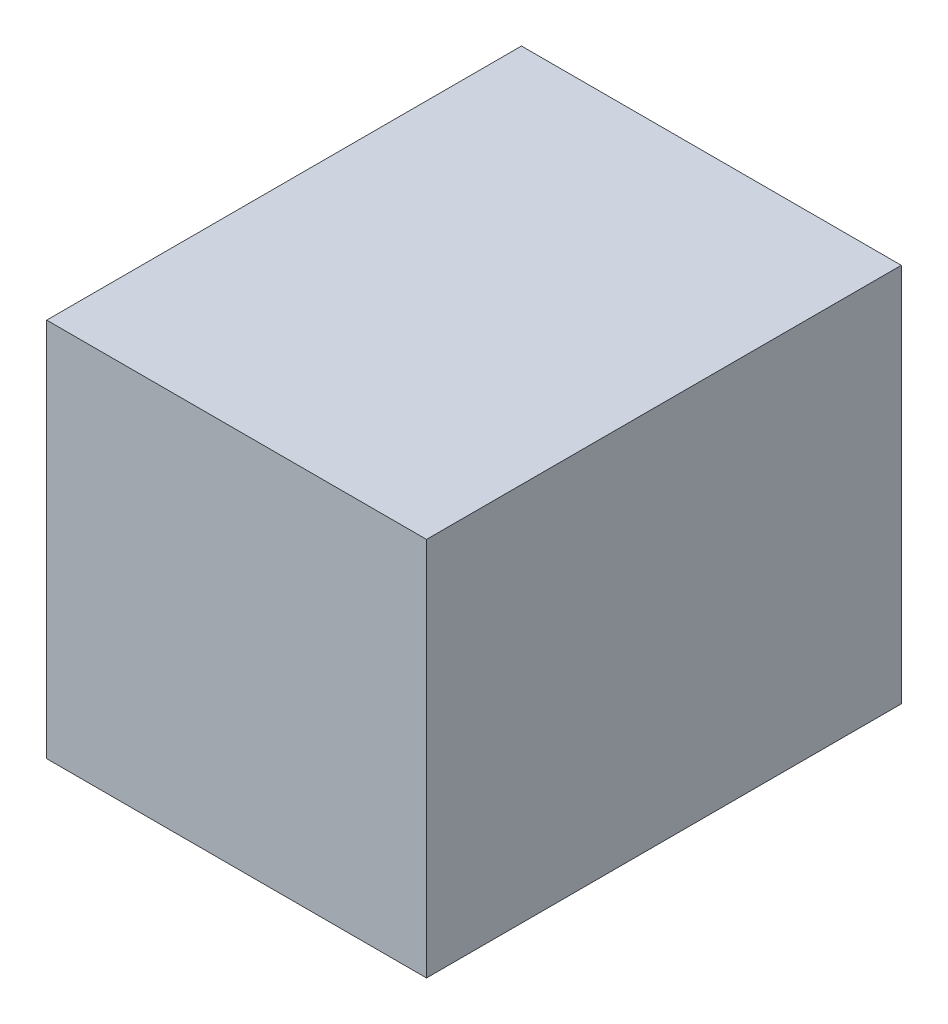
SolidWorks part; units mm, degrees
ref_plane "Front Plane" through (0, 0, 0) normal (0, 0, 1) x (1, 0, 0)
ref_plane "Top Plane" through (0, 0, 0) normal (0, 1, 0) x (1, 0, 0)
ref_plane "Right Plane" through (0, 0, 0) normal (1, 0, 0) x (0, 0, -1)
sketch "Sketch1" plane through (0, 0, 0) normal (0, 0, 1) x (1, 0, 0)
  line L1 (1.2774, -1.2645) -> (-1.1226, -1.2645)
  line L2 (1.2774, -1.2645) -> (1.2774, 1.1355)
  line L3 (1.2774, 1.1355) -> (-1.1226, 1.1355)
  line L4 (-1.1226, -1.2645) -> (-1.1226, 1.1355)
  dimension "D1" = 2.4
extrude "Boss-Extrude1" add sketch "Sketch1" along normal blind 3
